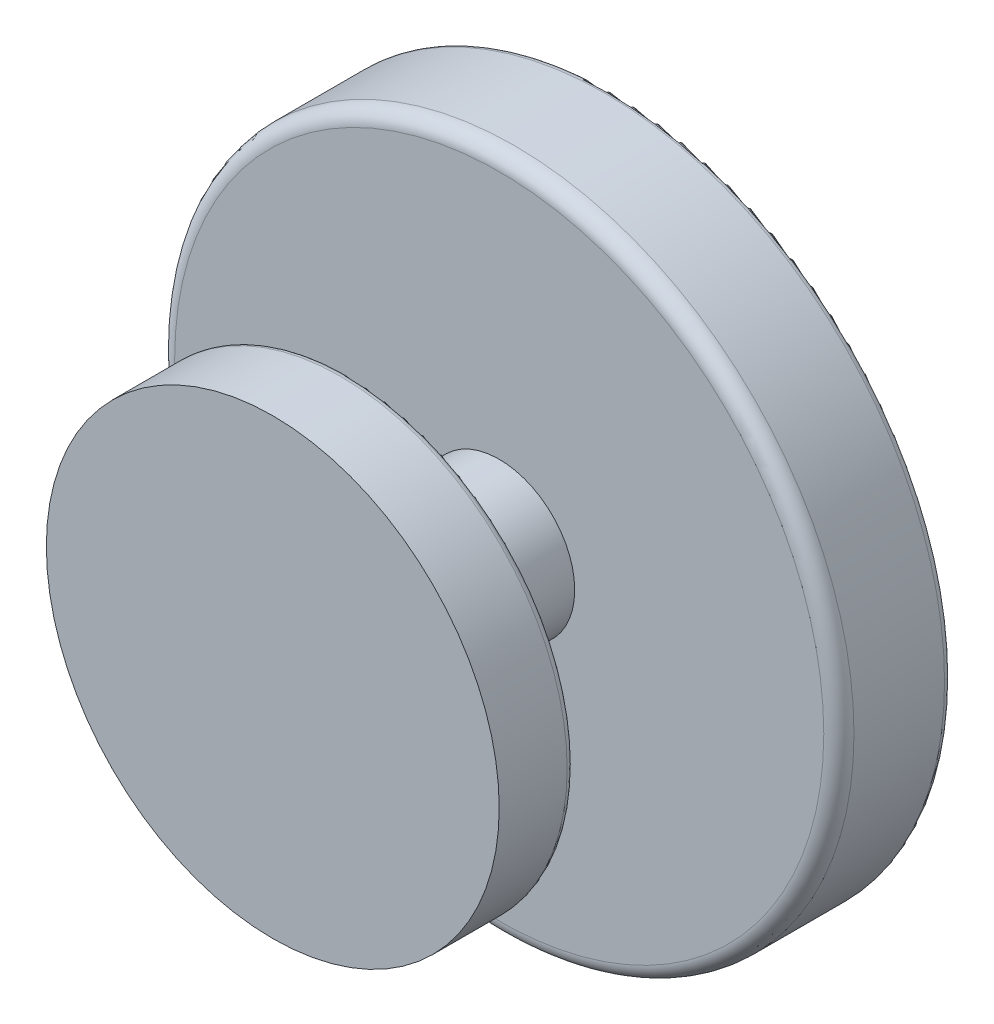
SolidWorks part; units mm, degrees
ref_plane "Plan de face" through (0, 0, 0) normal (0, 0, 1) x (1, 0, 0)
ref_plane "Plan de dessus" through (0, 0, 0) normal (0, 1, 0) x (1, 0, 0)
ref_plane "Plan de droite" through (0, 0, 0) normal (1, 0, 0) x (0, 0, -1)
sketch "Esquisse1" plane through (0, 0, 0) normal (0, 0, 1) x (1, 0, 0)
  circle A0 centre (0, 0) radius 45
  dimension "D1" = 90
extrude "Boss.-Extru.1" add sketch "Esquisse1" along normal blind 15
sketch "Esquisse3" plane through (0, 0, 15) normal (0, 0, 1) x (1, 0, 0)
  circle A0 centre (0, 0) radius 10
  dimension "D1" = 20
extrude "Boss.-Extru.2" add sketch "Esquisse3" along normal blind 20
sketch "Esquisse4" plane through (0, 0, 35) normal (0, 0, 1) x (1, 0, 0)
  circle A0 centre (0, 0) radius 30
  dimension "D1" = 60
extrude "Boss.-Extru.3" add sketch "Esquisse4" along normal blind 10
fillet "Congé1" radius 2 1 edges at (45, 0, 15)
sketch "Esquisse5" plane through (0, 0, 0) normal (0, 0, -1) x (-1, 0, 0)
  line L1 (-11.6, -2) -> (11.6, -2)
  line L2 (-11.6, -2) -> (-11.6, -33.8)
  line L3 (-11.6, -33.8) -> (11.6, -33.8)
  line L4 (11.6, -2) -> (11.6, -33.8)
  line L5 (-11.6, -2) -> (-11.6, 5.5)
  line L6 (11.6, -2) -> (11.6, 5.5)
  line L7 (-7.1, 10) -> (7.1, 10)
  arc A0 (-11.6, 5.5) -> (-7.1, 10) centre (-7.1, 5.5) cw
  arc A1 (7.1, 10) -> (11.6, 5.5) centre (7.1, 5.5) cw
  circle A2 centre (0, 0) radius 2.15
  dimension "D3" = 4.3
  dimension "D6" = 4.5
  dimension "D7" = 4.5
  dimension "D1" = 2
  dimension "D2" = 11.6
  dimension "D4" = 43.8
  dimension "D5" = 23.2
  dimension "D8" = 12
fillet "Congé2" radius 1 1 edges at (30, 0, 35)
fillet "Congé3" radius 1 1 edges at (45, 0, 0)
